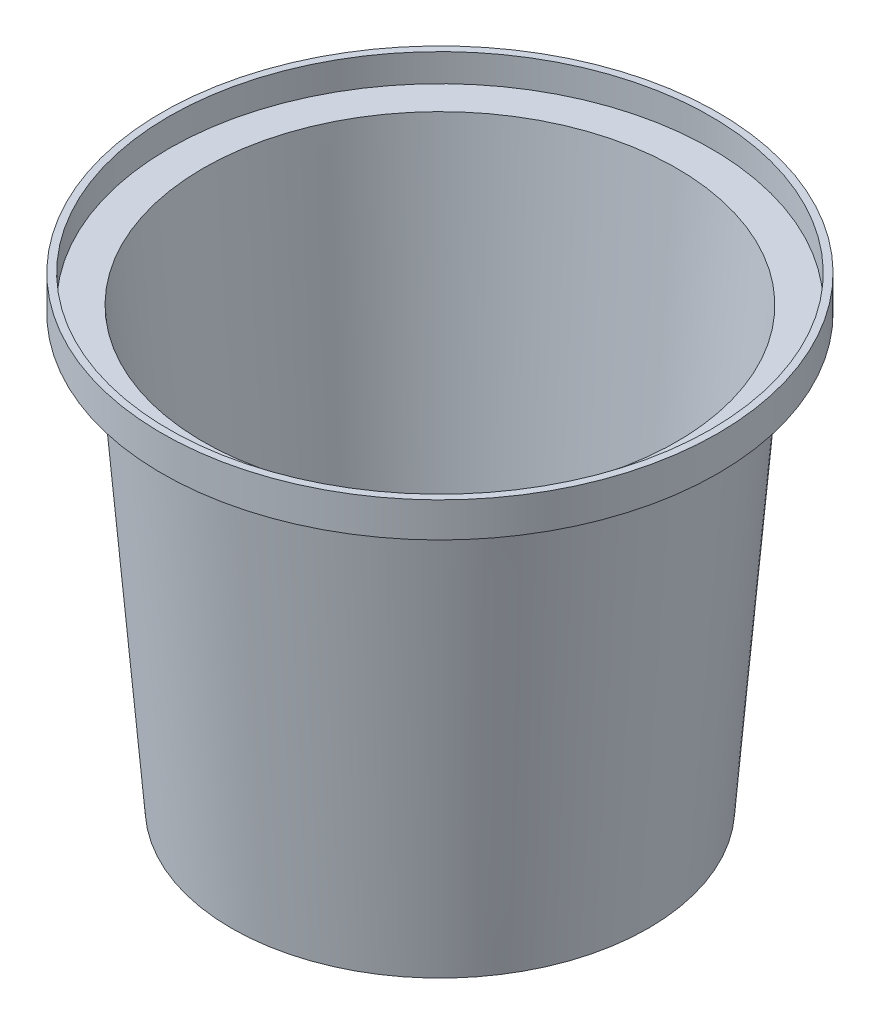
SolidWorks part; units mm, degrees
ref_plane "前视基准面" through (0, 0, 0) normal (0, 0, 1) x (1, 0, 0)
ref_plane "上视基准面" through (0, 0, 0) normal (0, 1, 0) x (1, 0, 0)
ref_plane "右视基准面" through (0, 0, 0) normal (1, 0, 0) x (0, 0, -1)
other "Configuration Table"
sketch "草图1" plane through (0, 0, 0) normal (0, 0, 1) x (1, 0, 0)
  line L0 (0, -878.9816) -> (0, 43070.0988) construction
  line L1 (0, 0) -> (-90, 0)
  line L2 (-90, 0) -> (-105, 185)
  line L3 (-105, 185) -> (-120, 185)
  line L4 (-120, 185) -> (-120, 200)
  line L5 (-120, 200) -> (0, 200)
  line L6 (0, 200) -> (0, 0)
  dimension "D1" = 240
  dimension "D2" = 15
  dimension "D3" = 200
  dimension "D4" = 180
  dimension "D5" = 15
revolve "旋转1" add sketch "草图1" angle 360 about L0
shell "抽壳1" thickness 3
